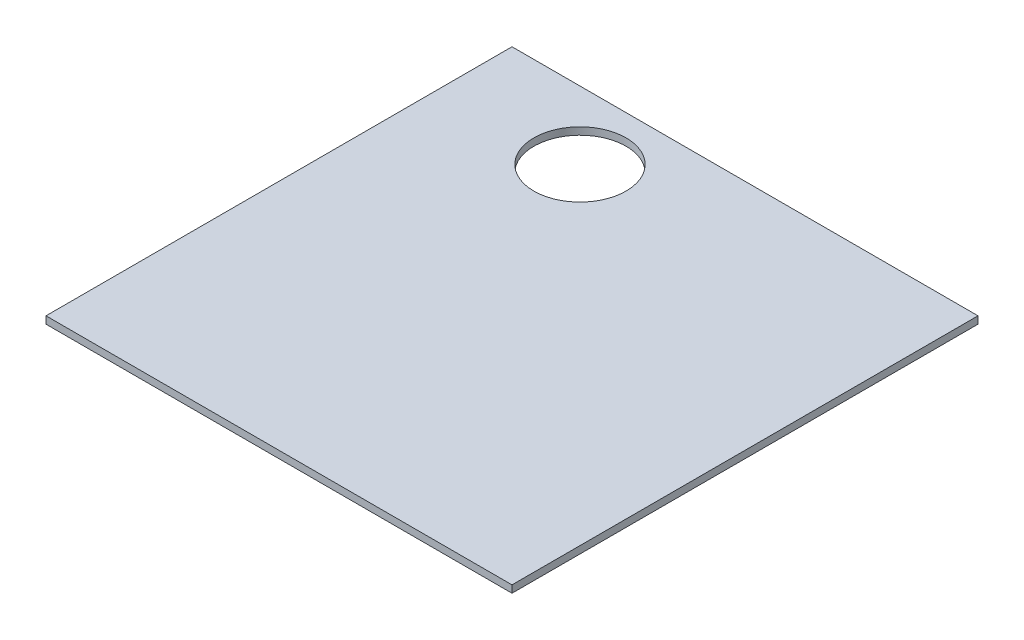
SolidWorks part; units mm, degrees
ref_plane "Front Plane" through (0, 0, 0) normal (0, 0, 1) x (1, 0, 0)
ref_plane "Top Plane" through (0, 0, 0) normal (0, 1, 0) x (1, 0, 0)
ref_plane "Right Plane" through (0, 0, 0) normal (1, 0, 0) x (0, 0, -1)
sketch "Sketch1" plane through (0, 0, 0) normal (0, 1, 0) x (1, 0, 0)
  line L1 (0, 0) -> (304.8, 0)
  line L2 (0, 0) -> (0, 304.8)
  line L3 (0, 304.8) -> (304.8, 304.8)
  line L4 (304.8, 0) -> (304.8, 304.8)
  dimension "D1" = 304.8
  dimension "D2" = 304.8
extrude "Boss-Extrude1" add sketch "Sketch1" along normal blind 4.7625
sketch "Sketch2" plane through (0, 4.7625, 0) normal (0, 1, 0) x (1, 0, 0)
  line L0 (304.8, 304.8) -> (0, 304.8) construction
  line L1 (0, 304.8) -> (0, 0) construction
  circle A0 centre (88.9, 260.35) radius 30.1625
  dimension "D1" = 44.45
  dimension "D2" = 88.9
extrude "Cut-Extrude1" cut sketch "Sketch2" against normal through all
